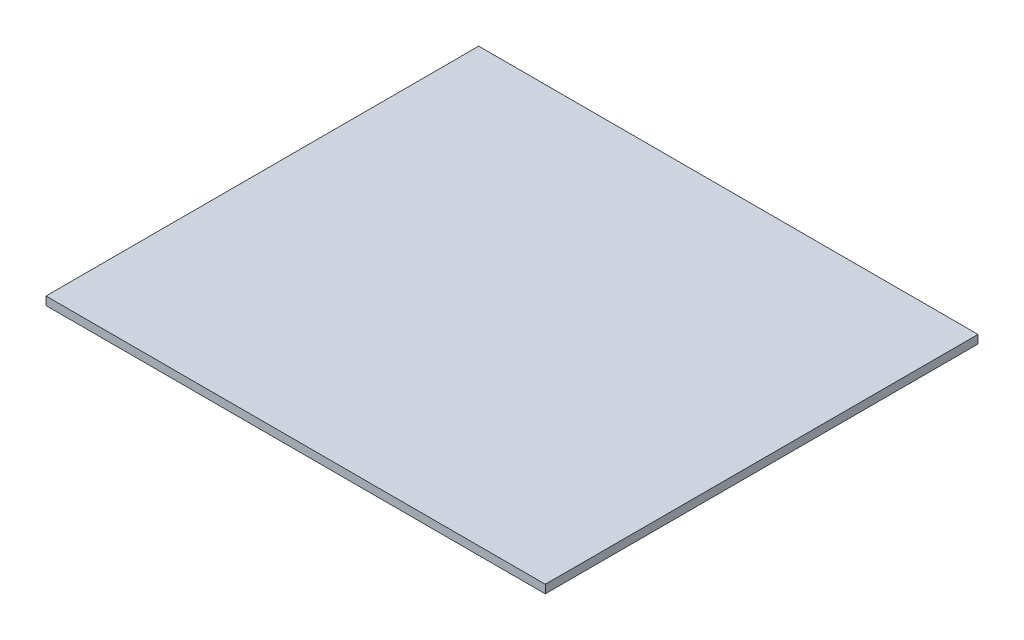
SolidWorks part; units mm, degrees
material "1060 Alloy"
ref_plane "Front Plane" through (0, 0, 0) normal (0, 0, 1) x (1, 0, 0)
ref_plane "Top Plane" through (0, 0, 0) normal (0, 1, 0) x (1, 0, 0)
ref_plane "Right Plane" through (0, 0, 0) normal (1, 0, 0) x (0, 0, -1)
sketch "Sketch1" plane through (0, 0, 0) normal (0, 1, 0) x (1, 0, 0)
  line L1 (150, -130) -> (-150, -130)
  line L2 (150, -130) -> (150, 130)
  line L3 (150, 130) -> (-150, 130)
  line L4 (-150, -130) -> (-150, 130)
  line L5 (150, -130) -> (-150, 130) construction
  line L6 (150, 130) -> (-150, -130) construction
  point P0 (0, 0)
  dimension "D1" = 300
  dimension "D2" = 260
extrude "Boss-Extrude1" add sketch "Sketch1" along normal blind 5
